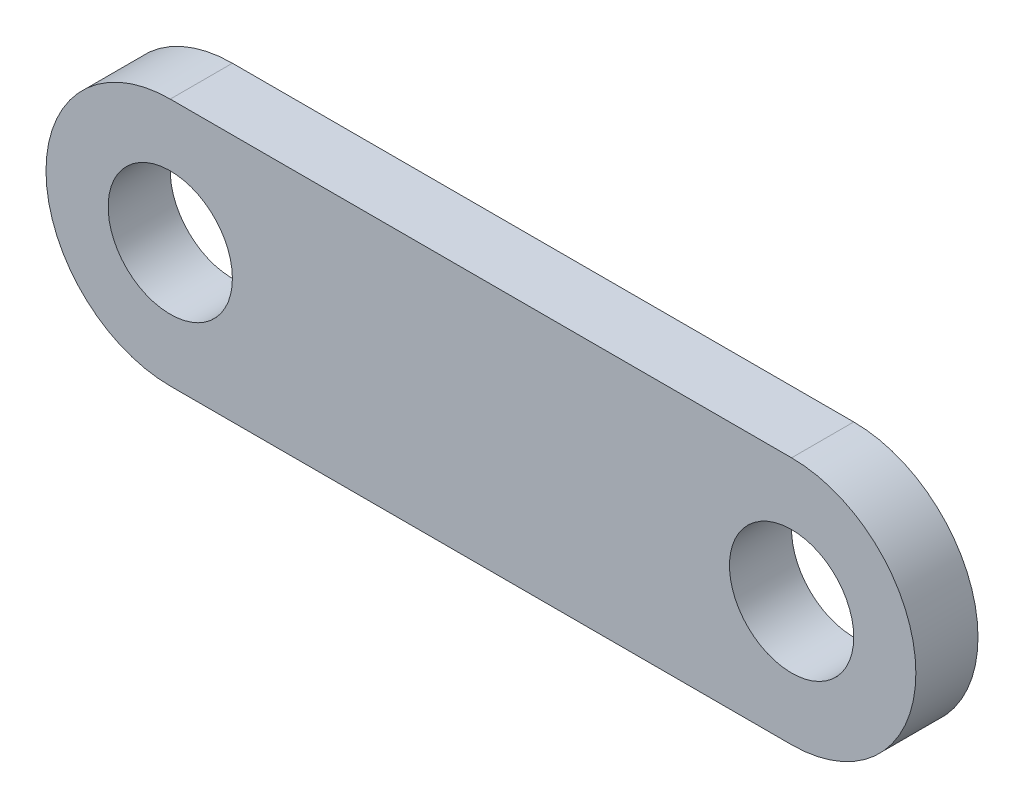
SolidWorks part; units mm, degrees
ref_plane "Front Plane" through (0, 0, 0) normal (0, 0, 1) x (1, 0, 0)
ref_plane "Top Plane" through (0, 0, 0) normal (0, 1, 0) x (1, 0, 0)
ref_plane "Right Plane" through (0, 0, 0) normal (1, 0, 0) x (0, 0, -1)
sketch "Sketch1" plane through (0, 0, 0) normal (0, 0, 1) x (1, 0, 0)
  line L0 (0, 0) -> (-25.4, 0) construction
  line L1 (0, -5.08) -> (-25.4, -5.08)
  line L2 (0, 5.08) -> (-25.4, 5.08)
  arc A0 (0, -5.08) -> (0, 5.08) centre (0, 0) ccw
  arc A1 (-25.4, 5.08) -> (-25.4, -5.08) centre (-25.4, 0) ccw
  circle A2 centre (-25.4, 0) radius 2.54
  circle A3 centre (0, 0) radius 2.54
  point P3 (-12.7, 0)
  dimension "D2" = 5.08
  dimension "D3" = 5.08
  dimension "D4" = 5.08
  dimension "D1" = 25.4
extrude "Boss-Extrude1" add sketch "Sketch1" along normal blind 2.54
